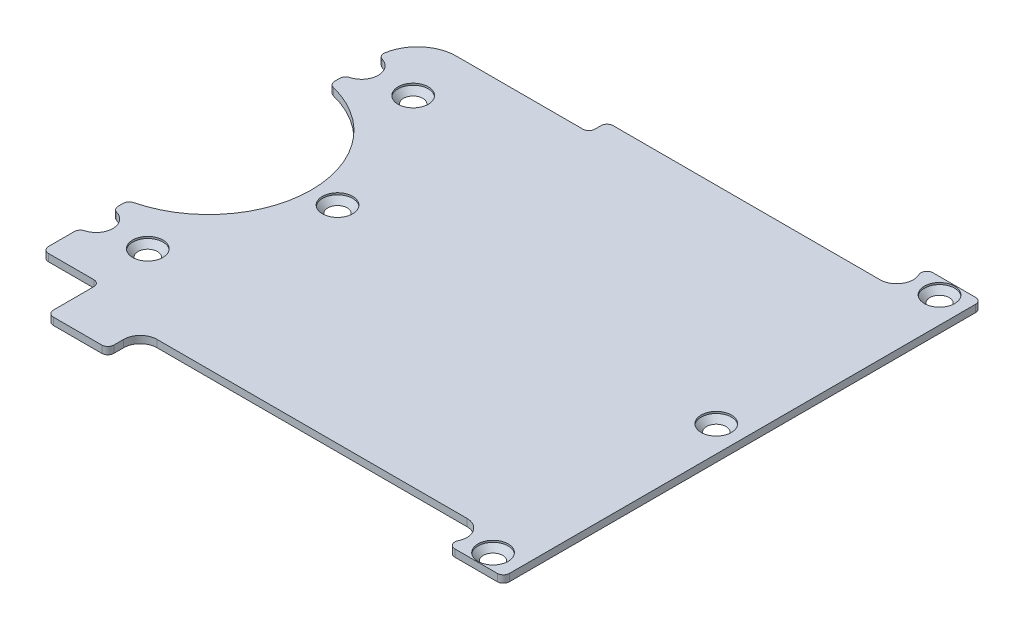
SolidWorks part; units mm, degrees
ref_plane "Front Plane" through (0, 0, 0) normal (0, 0, 1) x (1, 0, 0)
ref_plane "Top Plane" through (0, 0, 0) normal (0, 1, 0) x (1, 0, 0)
ref_plane "Right Plane" through (0, 0, 0) normal (1, 0, 0) x (0, 0, -1)
sketch "Sketch1" plane through (0, 0, 0) normal (0, 1, 0) x (1, 0, 0)
  line L0 (0, 30.3854) -> (0, -26.0557) construction
  line L1 (-19.0199, 0) -> (15.6179, 0) construction
  line L2 (-73.452, 57.1764) -> (-73.452, -39.7909) construction
  line L3 (0, 34.13) -> (-44.1, 34.13)
  line L4 (0, -34.13) -> (-51.202, -34.13)
  line L5 (-73.452, 19.17) -> (-73.452, 16.6626)
  line L6 (-53.952, -36.88) -> (-53.952, -39.5)
  line L7 (-63.952, -34.13) -> (-63.952, -39.5)
  line L8 (-73.452, -19.17) -> (-73.452, -16.6626)
  line L9 (11.4, 39.5) -> (11.4, -39.5)
  line L10 (11.4, 39.5) -> (0.8355, 39.5)
  line L11 (11.4, -39.5) -> (0.8355, -39.5)
  line L12 (-51.202, -34.13) -> (-73.452, -34.13) construction
  line L13 (-63.952, -39.5) -> (-52.0375, -39.5)
  line L14 (-73.452, -24.67) -> (-73.452, -30.8)
  line L15 (-63.952, 0) -> (-63.952, -34.13) construction
  line L16 (-73.452, -30.8) -> (-63.952, -30.8)
  line L17 (-63.952, -30.8) -> (-63.952, -34.13)
  line L18 (2.75, 36.88) -> (2.75, -36.88) construction
  line L19 (2.75, 36.88) -> (11.4, 36.88) construction
  line L20 (-73.452, 21.92) -> (11.4, 21.92) construction
  line L21 (7.075, 36.88) -> (7.075, -36.88) construction
  line L22 (-44.1, 34.13) -> (-44.1, -34.13) construction
  line L23 (-45.1, 33.13) -> (-45.1, 21.92) construction
  line L24 (-45.1, 33.13) -> (-44.1, 33.13) construction
  line L25 (-46.1, 31.13) -> (-66.992, 31.13)
  line L26 (-59.822, 0) -> (11.4, 0) construction
  line L27 (-73.452, 24.67) -> (-73.452, 31.13) construction
  line L28 (-45.1, 33.13) -> (-45.1, 32.13)
  line L29 (-24.211, 34.13) -> (-24.211, -34.13) construction
  circle A0 centre (0, 36.88) radius 2.5
  circle A1 centre (0, -36.88) radius 2.5
  circle A2 centre (-73.452, 21.92) radius 2.5
  circle A3 centre (-73.452, -21.92) radius 2.5
  circle A4 centre (-76.822, 0) radius 16
  circle A5 centre (-73.452, 21.92) radius 2.75
  circle A6 centre (-76.822, 0) radius 17
  circle A7 centre (-73.452, -21.92) radius 2.75
  circle A8 centre (0, 36.88) radius 2.75
  circle A9 centre (0, -36.88) radius 2.75
  arc A10 (-44.1, 34.13) -> (-45.1, 33.13) centre (-44.1, 33.13) ccw
  circle A11 centre (7.075, 36.88) radius 1
  circle A12 centre (7.075, -36.88) radius 1
  circle A13 centre (-64.925, 21.92) radius 1
  circle A14 centre (-64.925, -21.92) radius 1
  circle A15 centre (7.075, 0) radius 1
  circle A16 centre (-51.202, -36.88) radius 2.75
  arc A17 (-45.1, 32.13) -> (-46.1, 31.13) centre (-46.1, 32.13) cw
  arc A18 (-73.452, 24.67) -> (-66.992, 31.13) centre (-66.992, 24.67) cw
  circle A19 centre (-55.497, 0) radius 1
  point P39 (11.4, 0)
  point P77 (-59.822, 0)
  point P83 (-45.1, 31.13)
  point P86 (-24.211, 0)
  dimension "D2" = 5
  dimension "D3" = 43.84
  dimension "D5" = 32
  dimension "D16" = 2
  dimension "D20" = 1
  dimension "D1" = 73.76
  dimension "D4" = 74.96
  dimension "D6" = 3.37
  dimension "D12" = 79
  dimension "D13" = 11.4
  dimension "D9" = 10
  dimension "D10" = 55.5
  dimension "D11" = 5.37
  dimension "D14" = 8.7
  dimension "D15" = 9.5
  dimension "D17" = 72
  dimension "D18" = 1
  dimension "D7" = 0.25
  dimension "D8" = 1
extrude "Base shape" add sketch "Sketch1" along normal mid plane 1.2
fillet "Fillets" radius 1 14 edges at (-73.452, 0, -19.17) (-73.452, 0, -16.6626) (-73.452, 0, 24.67) (-73.452, 0, 19.17) (-73.452, 0, 16.6626) (-73.452, 0, 30.8) (-63.952, 0, 30.8) (0.8355, 0, -39.5) (0.8355, 0, 39.5) (11.4, 0, -39.5) (11.4, 0, 39.5) (-63.952, 0, 39.5) (-53.952, 0, 39.5) (-73.452, 0, -24.67)
hole_wizard "M2.5 countersunks" positions "Sketch2" profile "Sketch3" countersink size "M2" standard "ANSI Metric" end condition through all
sketch "Sketch2" plane through (0, -0.6, 0) normal (0, -1, 0) x (-1, 0, 0)
  point P0 (-7.075, 36.88)
  point P3 (-7.075, -36.88)
  point P6 (64.925, 21.92)
  point P9 (64.925, -21.92)
  point P13 (-7.075, 0)
  point P16 (55.497, 0)
sketch "Sketch3" plane through (7.075, -0.6, -36.88) normal (1, 0, 0) x (0, 0, -1)
  line L0 (0, 0) -> (0, 1.2)
  line L1 (0, 1.2) -> (1.25, 1.2)
  line L2 (1.25, 1.2) -> (1.25, 1.55)
  line L3 (1.25, 1.55) -> (2.5, 0.3)
  line L4 (2.5, 0.3) -> (2.5, 0)
  line L6 (2.5, 0) -> (0, 0)
  line L7 (-1.25, 1.55) -> (-2.5, 0.3) construction
  line L11 (0, -6.35) -> (0, 107.95) construction
  dimension "Thru Hole Dia." = 2.5
  dimension "Thru Hole Depth" = 1.2
  dimension "C'Sink Dia." = 5
  dimension "C'Sink Angle" = 90
  dimension "Head Clearance" = 0.3
mirror "Mirror1" about plane through (0, 0, 0) normal (0, 1, 0) of bodies 105
delete or keep bodies "Body-Delete/Keep 1" type delete bodies bodies 105
sketch "Sketch4" [suppressed] plane through (0, 0.5, 0) normal (0, 1, 0) x (1, 0, 0)
  line L13 (-73.452, 18.3058) -> (-73.452, 17.4615)
  line L14 (-73.452, -17.4615) -> (-73.452, -18.3058)
  line L15 (-73.452, -25.5342) -> (-73.452, -29.8)
  line L16 (-72.452, -30.8) -> (-64.952, -30.8)
  line L17 (-63.952, -31.8) -> (-63.952, -38.5)
  line L18 (-62.952, -39.5) -> (-54.952, -39.5)
  line L19 (-53.952, -38.5) -> (-53.952, -36.88)
  line L20 (-51.202, -34.13) -> (0, -34.13)
  line L21 (3.382, -39.5) -> (10.4, -39.5)
  line L22 (11.4, -38.5) -> (11.4, 38.5)
  line L23 (10.4, 39.5) -> (3.382, 39.5)
  line L24 (0, 34.13) -> (-42.6, 34.13)
  line L25 (-47.6, 29.13) -> (-68.992, 29.13)
  line L26 (-73.452, 18.3058) -> (-73.452, 17.4615)
  line L27 (-73.452, -17.4615) -> (-73.452, -18.3058)
  line L28 (-73.452, -25.5342) -> (-73.452, -29.8)
  line L29 (-72.452, -30.8) -> (-64.952, -30.8)
  line L30 (-63.952, -31.8) -> (-63.952, -38.5)
  line L31 (-62.952, -39.5) -> (-54.952, -39.5)
  line L32 (-53.952, -38.5) -> (-53.952, -36.88)
  line L33 (-51.202, -34.13) -> (0, -34.13)
  line L34 (3.382, -39.5) -> (10.4, -39.5)
  line L35 (11.4, -38.5) -> (11.4, 38.5)
  line L36 (10.4, 39.5) -> (3.382, 39.5)
  line L37 (0, 34.13) -> (-42.6, 34.13)
  line L38 (-47.6, 29.13) -> (-68.992, 29.13)
  circle A0 centre (-64.925, 21.92) radius 1 construction
  circle A1 centre (-55.822, 0) radius 1 construction
  circle A2 centre (-64.925, -21.92) radius 1 construction
  circle A3 centre (7.075, -36.88) radius 1 construction
  circle A4 centre (7.075, 0) radius 1 construction
  circle A5 centre (7.075, 36.88) radius 1 construction
  circle A6 centre (-64.925, 21.92) radius 1
  circle A7 centre (-55.822, 0) radius 1
  circle A8 centre (-64.925, -21.92) radius 1
  circle A9 centre (7.075, -36.88) radius 1
  circle A10 centre (7.075, 0) radius 1
  circle A11 centre (7.075, 36.88) radius 1
  arc A23 (-68.992, 29.13) -> (-73.3204, 25.7455) centre (-68.992, 24.67) ccw
  arc A24 (-73.3204, 25.7455) -> (-72.6438, 24.5486) centre (-72.3499, 25.5044) ccw
  arc A25 (-72.7187, 19.2696) -> (-72.6438, 24.5486) centre (-73.452, 21.92) ccw
  arc A26 (-72.7187, 19.2696) -> (-73.452, 18.3058) centre (-72.452, 18.3058) ccw
  arc A27 (-73.452, 17.4615) -> (-72.6948, 16.4914) centre (-72.452, 17.4615) ccw
  arc A28 (-72.6948, -16.4914) -> (-72.6948, 16.4914) centre (-76.822, 0) ccw
  arc A29 (-72.6948, -16.4914) -> (-73.452, -17.4615) centre (-72.452, -17.4615) ccw
  arc A30 (-73.452, -18.3058) -> (-72.7187, -19.2696) centre (-72.452, -18.3058) ccw
  arc A31 (-72.7187, -24.5704) -> (-72.7187, -19.2696) centre (-73.452, -21.92) ccw
  arc A32 (-72.7187, -24.5704) -> (-73.452, -25.5342) centre (-72.452, -25.5342) ccw
  arc A33 (-73.452, -29.8) -> (-72.452, -30.8) centre (-72.452, -29.8) ccw
  arc A34 (-63.952, -31.8) -> (-64.952, -30.8) centre (-64.952, -31.8) ccw
  arc A35 (-63.952, -38.5) -> (-62.952, -39.5) centre (-62.952, -38.5) ccw
  arc A36 (-54.952, -39.5) -> (-53.952, -38.5) centre (-54.952, -38.5) ccw
  arc A37 (-51.202, -34.13) -> (-53.952, -36.88) centre (-51.202, -36.88) ccw
  arc A38 (2.4802, -38.068) -> (0, -34.13) centre (0, -36.88) ccw
  arc A39 (2.4802, -38.068) -> (3.382, -39.5) centre (3.382, -38.5) ccw
  arc A40 (10.4, -39.5) -> (11.4, -38.5) centre (10.4, -38.5) ccw
  arc A41 (11.4, 38.5) -> (10.4, 39.5) centre (10.4, 38.5) ccw
  arc A42 (3.382, 39.5) -> (2.4802, 38.068) centre (3.382, 38.5) ccw
  arc A43 (0, 34.13) -> (2.4802, 38.068) centre (0, 36.88) ccw
  arc A44 (-42.6, 34.13) -> (-45.1, 31.63) centre (-42.6, 31.63) ccw
  arc A45 (-47.6, 29.13) -> (-45.1, 31.63) centre (-47.6, 31.63) ccw
  arc A46 (-68.992, 29.13) -> (-73.3204, 25.7455) centre (-68.992, 24.67) ccw
  arc A47 (-73.3204, 25.7455) -> (-72.6438, 24.5486) centre (-72.3499, 25.5044) ccw
  arc A48 (-72.7187, 19.2696) -> (-72.6438, 24.5486) centre (-73.452, 21.92) ccw
  arc A49 (-72.7187, 19.2696) -> (-73.452, 18.3058) centre (-72.452, 18.3058) ccw
  arc A50 (-73.452, 17.4615) -> (-72.6948, 16.4914) centre (-72.452, 17.4615) ccw
  arc A51 (-72.6948, -16.4914) -> (-72.6948, 16.4914) centre (-76.822, 0) ccw
  arc A52 (-72.6948, -16.4914) -> (-73.452, -17.4615) centre (-72.452, -17.4615) ccw
  arc A53 (-73.452, -18.3058) -> (-72.7187, -19.2696) centre (-72.452, -18.3058) ccw
  arc A54 (-72.7187, -24.5704) -> (-72.7187, -19.2696) centre (-73.452, -21.92) ccw
  arc A55 (-72.7187, -24.5704) -> (-73.452, -25.5342) centre (-72.452, -25.5342) ccw
  arc A56 (-73.452, -29.8) -> (-72.452, -30.8) centre (-72.452, -29.8) ccw
  arc A57 (-63.952, -31.8) -> (-64.952, -30.8) centre (-64.952, -31.8) ccw
  arc A58 (-63.952, -38.5) -> (-62.952, -39.5) centre (-62.952, -38.5) ccw
  arc A59 (-54.952, -39.5) -> (-53.952, -38.5) centre (-54.952, -38.5) ccw
  arc A60 (-51.202, -34.13) -> (-53.952, -36.88) centre (-51.202, -36.88) ccw
  arc A61 (2.4802, -38.068) -> (0, -34.13) centre (0, -36.88) ccw
  arc A62 (2.4802, -38.068) -> (3.382, -39.5) centre (3.382, -38.5) ccw
  arc A63 (10.4, -39.5) -> (11.4, -38.5) centre (10.4, -38.5) ccw
  arc A64 (11.4, 38.5) -> (10.4, 39.5) centre (10.4, 38.5) ccw
  arc A65 (3.382, 39.5) -> (2.4802, 38.068) centre (3.382, 38.5) ccw
  arc A66 (0, 34.13) -> (2.4802, 38.068) centre (0, 36.88) ccw
  arc A67 (-42.6, 34.13) -> (-45.1, 31.63) centre (-42.6, 31.63) ccw
  arc A68 (-47.6, 29.13) -> (-45.1, 31.63) centre (-47.6, 31.63) ccw
  dimension "D1" = 0
extrude "Core fill" [suppressed] add sketch "Sketch4" along normal offset from surface (9.2 mm away) 10.2
sketch "Sketch5" [suppressed] plane through (0, 9.45, 0) normal (0, 1, 0) x (1, 0, 0)
  line L0 (-46.1, 30.43) -> (-66.992, 30.43)
  line L1 (-72.752, 18.3058) -> (-72.752, 17.4615)
  line L2 (-72.752, -17.4615) -> (-72.752, -18.3058)
  line L3 (-72.752, -25.5342) -> (-72.752, -29.8)
  line L4 (-72.452, -30.1) -> (-64.952, -30.1)
  line L5 (-63.252, -31.8) -> (-63.252, -38.5)
  line L6 (-62.952, -38.8) -> (-54.952, -38.8)
  line L7 (-54.652, -38.5) -> (-54.652, -36.88)
  line L8 (-51.202, -33.43) -> (0, -33.43)
  line L9 (3.382, -38.8) -> (10.4, -38.8)
  line L10 (10.7, -38.5) -> (10.7, 38.5)
  line L11 (10.4, 38.8) -> (3.382, 38.8)
  line L12 (0, 33.43) -> (-44.1, 33.43)
  line L13 (-46.1, 31.13) -> (-66.992, 31.13)
  line L14 (-73.452, 18.3058) -> (-73.452, 17.4615)
  line L15 (-73.452, -17.4615) -> (-73.452, -18.3058)
  line L16 (-73.452, -25.5342) -> (-73.452, -29.8)
  line L17 (-72.452, -30.8) -> (-64.952, -30.8)
  line L18 (-63.952, -31.8) -> (-63.952, -38.5)
  line L19 (-62.952, -39.5) -> (-54.952, -39.5)
  line L20 (-53.952, -38.5) -> (-53.952, -36.88)
  line L21 (-51.202, -34.13) -> (0, -34.13)
  line L22 (3.382, -39.5) -> (10.4, -39.5)
  line L23 (11.4, -38.5) -> (11.4, 38.5)
  line L24 (10.4, 39.5) -> (3.382, 39.5)
  line L25 (0, 34.13) -> (-44.1, 34.13)
  line L26 (-46.1, 31.13) -> (-66.992, 31.13)
  line L27 (-73.452, 18.3058) -> (-73.452, 17.4615)
  line L28 (-73.452, -17.4615) -> (-73.452, -18.3058)
  line L29 (-73.452, -25.5342) -> (-73.452, -29.8)
  line L30 (-72.452, -30.8) -> (-64.952, -30.8)
  line L31 (-63.952, -31.8) -> (-63.952, -38.5)
  line L32 (-62.952, -39.5) -> (-54.952, -39.5)
  line L33 (-53.952, -38.5) -> (-53.952, -36.88)
  line L34 (-51.202, -34.13) -> (0, -34.13)
  line L35 (3.382, -39.5) -> (10.4, -39.5)
  line L36 (11.4, -38.5) -> (11.4, 38.5)
  line L37 (10.4, 39.5) -> (3.382, 39.5)
  line L38 (0, 34.13) -> (-44.1, 34.13)
  line L39 (-66.992, 31.13) -> (-66.992, 30.43) construction
  line L40 (-63.025, 21.92) -> (-62.325, 21.92) construction
  line L41 (-67.525, 21.92) -> (-70.002, 21.92) construction
  line L42 (-64.925, 24.52) -> (-64.925, 30.43) construction
  line L43 (-64.925, 19.32) -> (-64.925, 13.1054) construction
  line L44 (-65.275, 30.4537) -> (-64.575, 30.4537)
  line L45 (-65.275, 30.4537) -> (-65.275, 24.4963)
  line L46 (-65.275, 24.4963) -> (-64.575, 24.4963)
  line L47 (-64.575, 30.4537) -> (-64.575, 24.4963)
  line L48 (-65.275, 30.4537) -> (-64.575, 24.4963) construction
  line L49 (-65.275, 24.4963) -> (-64.575, 30.4537) construction
  line L50 (-70.0257, 22.27) -> (-67.5013, 22.27)
  line L51 (-70.0257, 22.27) -> (-70.0257, 21.57)
  line L52 (-70.0257, 21.57) -> (-67.5013, 21.57)
  line L53 (-67.5013, 22.27) -> (-67.5013, 21.57)
  line L54 (-70.0257, 22.27) -> (-67.5013, 21.57) construction
  line L55 (-70.0257, 21.57) -> (-67.5013, 22.27) construction
  line L56 (-10.5773, 0) -> (21.3129, 0) construction
  line L57 (-65.275, 19.6465) -> (-64.575, 19.6465)
  line L58 (-65.275, 19.6465) -> (-65.275, 12.7789)
  line L59 (-65.275, 12.7789) -> (-64.575, 12.7789)
  line L60 (-64.575, 19.6465) -> (-64.575, 12.7789)
  line L61 (-65.275, 19.6465) -> (-64.575, 12.7789) construction
  line L62 (-65.275, 12.7789) -> (-64.575, 19.6465) construction
  line L63 (4.475, 36.88) -> (3.45, 36.88) construction
  line L68 (-52.897, 0) -> (4.475, 0) construction
  line L69 (-24.211, 0) -> (-24.211, 33.43) construction
  line L70 (9.675, 36.88) -> (10.7, 36.88) construction
  line L71 (-55.497, 2.6) -> (-59.314, 2.6)
  line L72 (3.4263, 37.23) -> (4.4987, 37.23)
  line L73 (3.4263, 37.23) -> (3.4263, 36.53)
  line L74 (3.4263, 36.53) -> (4.4987, 36.53)
  line L75 (4.4987, 37.23) -> (4.4987, 36.53)
  line L76 (3.4263, 37.23) -> (4.4987, 36.53) construction
  line L77 (3.4263, 36.53) -> (4.4987, 37.23) construction
  line L78 (10.7237, 37.23) -> (9.6513, 37.23)
  line L79 (10.7237, 37.23) -> (10.7237, 36.53)
  line L80 (10.7237, 36.53) -> (9.6513, 36.53)
  line L81 (9.6513, 37.23) -> (9.6513, 36.53)
  line L82 (10.7237, 37.23) -> (9.6513, 36.53) construction
  line L83 (10.7237, 36.53) -> (9.6513, 37.23) construction
  line L84 (-59.2243, 1.9) -> (-57.2718, 1.9)
  line L85 (10.7237, -36.53) -> (9.6513, -36.53)
  line L86 (10.7237, -37.23) -> (9.6513, -37.23)
  line L87 (3.4263, -37.23) -> (4.4987, -37.23)
  line L88 (3.4263, -36.53) -> (4.4987, -36.53)
  line L89 (-70.0257, -22.27) -> (-67.5013, -22.27)
  line L90 (-70.0257, -21.57) -> (-67.5013, -21.57)
  line L91 (-65.275, -19.6465) -> (-65.275, -12.7789)
  line L92 (-64.575, -19.6465) -> (-64.575, -12.7789)
  line L93 (-64.925, -21.92) -> (-64.952, -31.8) construction
  line L95 (-55.497, -2.6) -> (-59.314, -2.6)
  line L96 (-59.2243, -1.9) -> (-57.2718, -1.9)
  line L97 (-65.2898, -30.139) -> (-64.5898, -30.139)
  line L98 (-65.2898, -30.139) -> (-65.2898, -24.4983)
  line L99 (-65.2898, -24.4983) -> (-64.5898, -24.4983)
  line L100 (-64.5898, -30.139) -> (-64.5898, -24.4983)
  line L101 (-65.2898, -30.139) -> (-64.5898, -24.4983) construction
  line L102 (-65.2898, -24.4983) -> (-64.5898, -30.139) construction
  line L105 (4.4987, -0.35) -> (-52.9207, -0.35)
  line L106 (4.4987, -0.35) -> (4.4987, 0.35)
  line L107 (4.4987, 0.35) -> (-52.9207, 0.35)
  line L108 (-52.9207, -0.35) -> (-52.9207, 0.35)
  line L109 (4.4987, -0.35) -> (-52.9207, 0.35) construction
  line L110 (4.4987, 0.35) -> (-52.9207, -0.35) construction
  line L111 (7.075, 2.6) -> (10.892, 2.6)
  line L112 (10.8023, 1.9) -> (8.8498, 1.9)
  line L113 (10.8023, -1.9) -> (8.8498, -1.9)
  line L114 (7.075, -2.6) -> (10.892, -2.6)
  line L115 (-45.1, 33.13) -> (-45.1, 32.13) construction
  line L116 (-45.1, 33.13) -> (-45.1, 32.13)
  line L118 (-45.1, 33.13) -> (-45.1, 32.13)
  line L119 (-44.4, 33.13) -> (-44.4, 32.13)
  circle A0 centre (-64.925, 21.92) radius 1.9
  arc A1 (-66.992, 30.43) -> (-72.6826, 25.5618) centre (-66.992, 24.67) ccw
  arc A2 (-72.6826, 25.5618) -> (-72.4715, 25.2277) centre (-72.3862, 25.5153) ccw
  arc A3 (-72.532, 18.5949) -> (-72.4715, 25.2277) centre (-73.452, 21.92) ccw
  arc A4 (-72.532, 18.5949) -> (-72.752, 18.3058) centre (-72.452, 18.3058) ccw
  arc A5 (-72.752, 17.4615) -> (-72.5249, 17.1705) centre (-72.452, 17.4615) ccw
  arc A6 (-72.5249, -17.1705) -> (-72.5249, 17.1705) centre (-76.822, 0) ccw
  arc A7 (-72.5249, -17.1705) -> (-72.752, -17.4615) centre (-72.452, -17.4615) ccw
  arc A8 (-72.752, -18.3058) -> (-72.532, -18.5949) centre (-72.452, -18.3058) ccw
  arc A9 (-72.532, -25.2451) -> (-72.532, -18.5949) centre (-73.452, -21.92) ccw
  arc A10 (-72.532, -25.2451) -> (-72.752, -25.5342) centre (-72.452, -25.5342) ccw
  arc A11 (-72.752, -29.8) -> (-72.452, -30.1) centre (-72.452, -29.8) ccw
  arc A12 (-63.252, -31.8) -> (-64.952, -30.1) centre (-64.952, -31.8) ccw
  arc A13 (-63.252, -38.5) -> (-62.952, -38.8) centre (-62.952, -38.5) ccw
  arc A14 (-54.952, -38.8) -> (-54.652, -38.5) centre (-54.952, -38.5) ccw
  arc A15 (-51.202, -33.43) -> (-54.652, -36.88) centre (-51.202, -36.88) ccw
  arc A16 (3.1115, -38.3704) -> (0, -33.43) centre (0, -36.88) ccw
  arc A17 (3.1115, -38.3704) -> (3.382, -38.8) centre (3.382, -38.5) ccw
  arc A18 (10.4, -38.8) -> (10.7, -38.5) centre (10.4, -38.5) ccw
  arc A19 (10.7, 38.5) -> (10.4, 38.8) centre (10.4, 38.5) ccw
  arc A20 (3.382, 38.8) -> (3.1115, 38.3704) centre (3.382, 38.5) ccw
  arc A21 (0, 33.43) -> (3.1115, 38.3704) centre (0, 36.88) ccw
  arc A23 (-66.992, 31.13) -> (-73.3741, 25.6702) centre (-66.992, 24.67) ccw
  arc A24 (-73.3741, 25.6702) -> (-72.6704, 24.5566) centre (-72.3862, 25.5153) ccw
  arc A25 (-72.7187, 19.2696) -> (-72.6704, 24.5566) centre (-73.452, 21.92) ccw
  arc A26 (-72.7187, 19.2696) -> (-73.452, 18.3058) centre (-72.452, 18.3058) ccw
  arc A27 (-73.452, 17.4615) -> (-72.6948, 16.4914) centre (-72.452, 17.4615) ccw
  arc A28 (-72.6948, -16.4914) -> (-72.6948, 16.4914) centre (-76.822, 0) ccw
  arc A29 (-72.6948, -16.4914) -> (-73.452, -17.4615) centre (-72.452, -17.4615) ccw
  arc A30 (-73.452, -18.3058) -> (-72.7187, -19.2696) centre (-72.452, -18.3058) ccw
  arc A31 (-72.7187, -24.5704) -> (-72.7187, -19.2696) centre (-73.452, -21.92) ccw
  arc A32 (-72.7187, -24.5704) -> (-73.452, -25.5342) centre (-72.452, -25.5342) ccw
  arc A33 (-73.452, -29.8) -> (-72.452, -30.8) centre (-72.452, -29.8) ccw
  arc A34 (-63.952, -31.8) -> (-64.952, -30.8) centre (-64.952, -31.8) ccw
  arc A35 (-63.952, -38.5) -> (-62.952, -39.5) centre (-62.952, -38.5) ccw
  arc A36 (-54.952, -39.5) -> (-53.952, -38.5) centre (-54.952, -38.5) ccw
  arc A37 (-51.202, -34.13) -> (-53.952, -36.88) centre (-51.202, -36.88) ccw
  arc A38 (2.4802, -38.068) -> (0, -34.13) centre (0, -36.88) ccw
  arc A39 (2.4802, -38.068) -> (3.382, -39.5) centre (3.382, -38.5) ccw
  arc A40 (10.4, -39.5) -> (11.4, -38.5) centre (10.4, -38.5) ccw
  arc A41 (11.4, 38.5) -> (10.4, 39.5) centre (10.4, 38.5) ccw
  arc A42 (3.382, 39.5) -> (2.4802, 38.068) centre (3.382, 38.5) ccw
  arc A43 (0, 34.13) -> (2.4802, 38.068) centre (0, 36.88) ccw
  arc A44 (-44.1, 34.13) -> (-45.1, 33.13) centre (-44.1, 33.13) ccw
  arc A45 (-46.1, 31.13) -> (-45.1, 32.13) centre (-46.1, 32.13) ccw
  arc A46 (-66.992, 31.13) -> (-73.3741, 25.6702) centre (-66.992, 24.67) ccw
  arc A47 (-73.3741, 25.6702) -> (-72.6704, 24.5566) centre (-72.3862, 25.5153) ccw
  arc A48 (-72.7187, 19.2696) -> (-72.6704, 24.5566) centre (-73.452, 21.92) ccw
  arc A49 (-72.7187, 19.2696) -> (-73.452, 18.3058) centre (-72.452, 18.3058) ccw
  arc A50 (-73.452, 17.4615) -> (-72.6948, 16.4914) centre (-72.452, 17.4615) ccw
  arc A51 (-72.6948, -16.4914) -> (-72.6948, 16.4914) centre (-76.822, 0) ccw
  arc A52 (-72.6948, -16.4914) -> (-73.452, -17.4615) centre (-72.452, -17.4615) ccw
  arc A53 (-73.452, -18.3058) -> (-72.7187, -19.2696) centre (-72.452, -18.3058) ccw
  arc A54 (-72.7187, -24.5704) -> (-72.7187, -19.2696) centre (-73.452, -21.92) ccw
  arc A55 (-72.7187, -24.5704) -> (-73.452, -25.5342) centre (-72.452, -25.5342) ccw
  arc A56 (-73.452, -29.8) -> (-72.452, -30.8) centre (-72.452, -29.8) ccw
  arc A57 (-63.952, -31.8) -> (-64.952, -30.8) centre (-64.952, -31.8) ccw
  arc A58 (-63.952, -38.5) -> (-62.952, -39.5) centre (-62.952, -38.5) ccw
  arc A59 (-54.952, -39.5) -> (-53.952, -38.5) centre (-54.952, -38.5) ccw
  arc A60 (-51.202, -34.13) -> (-53.952, -36.88) centre (-51.202, -36.88) ccw
  arc A61 (2.4802, -38.068) -> (0, -34.13) centre (0, -36.88) ccw
  arc A62 (2.4802, -38.068) -> (3.382, -39.5) centre (3.382, -38.5) ccw
  arc A63 (10.4, -39.5) -> (11.4, -38.5) centre (10.4, -38.5) ccw
  arc A64 (11.4, 38.5) -> (10.4, 39.5) centre (10.4, 38.5) ccw
  arc A65 (3.382, 39.5) -> (2.4802, 38.068) centre (3.382, 38.5) ccw
  arc A66 (0, 34.13) -> (2.4802, 38.068) centre (0, 36.88) ccw
  circle A70 centre (-64.925, 21.92) radius 2.6
  circle A71 centre (-55.497, 0) radius 1.9
  circle A73 centre (7.075, 0) radius 1.9
  circle A74 centre (7.075, 36.88) radius 1.9
  circle A76 centre (7.075, 36.88) radius 2.6
  circle A77 centre (7.075, 0) radius 2.6
  circle A80 centre (-55.497, 0) radius 2.6
  circle A81 centre (7.075, -36.88) radius 2.6
  circle A82 centre (7.075, -36.88) radius 1.9
  circle A83 centre (-64.925, -21.92) radius 1.9
  circle A84 centre (-64.925, -21.92) radius 2.6
  arc A92 (-46.1, 31.13) -> (-45.1, 32.13) centre (-46.1, 32.13) ccw construction
  arc A93 (-44.1, 34.13) -> (-45.1, 33.13) centre (-44.1, 33.13) ccw construction
  arc A94 (-46.1, 31.13) -> (-45.1, 32.13) centre (-46.1, 32.13) ccw
  arc A95 (-44.1, 34.13) -> (-45.1, 33.13) centre (-44.1, 33.13) ccw
  arc A96 (-44.1, 33.43) -> (-44.4, 33.13) centre (-44.1, 33.13) ccw
  arc A97 (-46.1, 30.43) -> (-44.4, 32.13) centre (-46.1, 32.13) ccw
  arc A108 (-46.1, 31.13) -> (-45.1, 33.13) centre (-46.1, 32.38) ccw construction
  arc A110 (-46.1, 30.43) -> (-44.3651, 33.2704) centre (-46.1, 32.38) ccw construction
  arc A111 (-44.1, 33.43) -> (-44.3651, 33.2704) centre (-44.1, 33.13) ccw construction
  arc A115 (-44.1, 34.13) -> (-45.1, 33.13) centre (-44.1, 33.13) ccw construction
  point P129 (-64.925, 27.475)
  point P145 (-68.7635, 21.92)
  point P152 (-64.925, 16.2127)
  point P162 (-24.211, 0)
  point P169 (3.9625, 36.88)
  point P174 (10.1875, 36.88)
  point P183 (-64.9398, -27.3187)
  point P185 (-55.497, 1.9)
  dimension "D2" = 3.75
  dimension "D1" = 0
  dimension "D3" = 0.7
extrude "Core walls" [suppressed] cut sketch "Sketch5" against normal up to next
sketch "Sketch6" [suppressed] plane through (0, -0.75, 0) normal (0, -1, 0) x (1, 0, 0)
  line L0 (-62.952, 38.8) -> (-54.952, 38.8) construction
  line L1 (-60.252, 38.8) -> (-63.252, 38.8)
  line L2 (-60.252, 38.8) -> (-60.252, 31.8)
  line L3 (-60.252, 31.8) -> (-63.252, 31.8)
  line L4 (-63.252, 38.8) -> (-63.252, 31.8)
  dimension "D1" = 3
extrude "XT30 fill" [suppressed] add sketch "Sketch6" against normal up to surface (10.2 mm away)
sketch "Sketch7" [suppressed] plane through (-63.952, 0, 0) normal (-1, 0, 0) x (0, 0, 1)
  line L0 (31.8, 9.45) -> (38.5, 9.45) construction
  line L1 (38.2, 9.45) -> (32.6, 9.45)
  line L2 (38.2, 9.45) -> (38.2, -0.75)
  line L3 (38.2, -0.75) -> (32.6, -0.75)
  line L4 (32.6, 9.45) -> (32.6, -0.75)
  line L5 (31.8, -0.75) -> (38.5, -0.75) construction
  line L6 (39.5, 9.45) -> (39.5, -0.75) construction
  line L7 (32.6, 0.25) -> (33.6, -0.75)
  line L8 (35.4, 9.45) -> (35.4, -0.75) construction
  line L9 (38.2, 0.25) -> (37.2, -0.75)
  line L11 (33.3, -0.45) -> (37.5, -0.45)
  line L12 (33.3, -0.45) -> (33.3, -0.75)
  line L13 (33.3, -0.75) -> (37.5, -0.75)
  line L14 (37.5, -0.45) -> (37.5, -0.75)
  line L15 (33.3, -0.45) -> (37.5, -0.75) construction
  line L16 (33.3, -0.75) -> (37.5, -0.45) construction
  point P16 (35.4, -0.6)
  line M9 (38.5, 9.45) -> (31.8, 9.45)
  dimension "D1" = 5.6
  dimension "D2" = 1.3
  dimension "D3" = 45
  dimension "D4" = 1
  dimension "D5" = 0.7
extrude "XT30 cut" [suppressed] cut sketch "Sketch7" against normal up to next contours L7 L11 L9 L2 L4 M9
sketch "Sketch8" [suppressed] plane through (0, -0.75, 0) normal (0, -1, 0) x (1, 0, 0)
  line L0 (-63.252, 31.8) -> (-63.252, 32.6) construction
  line L1 (-60.252, 31.8) -> (-59.452, 31.8)
  line L2 (-60.252, 31.8) -> (-60.252, 33.3)
  line L3 (-60.252, 33.3) -> (-59.452, 33.3)
  line L4 (-59.452, 31.8) -> (-59.452, 33.3)
  line L5 (-60.252, 32.6) -> (-63.952, 32.6) construction
  line L6 (-60.252, 33.3) -> (-63.952, 33.3) construction
  line L7 (-60.252, 37.5) -> (-63.952, 37.5) construction
  line L9 (-60.252, 38.8) -> (-59.452, 38.8)
  line L10 (-60.252, 38.8) -> (-60.252, 37.5)
  line L11 (-60.252, 37.5) -> (-59.452, 37.5)
  line L12 (-59.452, 38.8) -> (-59.452, 37.5)
extrude "XT30 rear support" [suppressed] add sketch "Sketch8" against normal up to surface (10.2 mm away)
sketch "Sketch9" [suppressed] plane through (0, -0.75, 0) normal (0, -1, 0) x (1, 0, 0)
  line L0 (-63.952, 38.2) -> (-63.952, 32.6)
  line L1 (-44.4, -34.0839) -> (-44.4, 34.13)
  line L2 (-63.952, 31.8) -> (-63.952, 32.6) construction
  line L3 (-63.952, 38.2) -> (-63.952, 38.5) construction
  line L4 (-62.952, 39.5) -> (-54.952, 39.5) construction
  line L5 (-53.952, 38.5) -> (-53.952, 36.88) construction
  line L6 (-51.202, 34.13) -> (0, 34.13) construction
  line L7 (3.382, 39.5) -> (10.4, 39.5) construction
  line L8 (11.4, 38.5) -> (11.4, -38.5) construction
  line L9 (10.4, -39.5) -> (3.382, -39.5) construction
  line L10 (0, -34.13) -> (-44.1, -34.13) construction
  line L11 (-46.1, -31.13) -> (-66.992, -31.13) construction
  line L12 (-73.452, -18.3058) -> (-73.452, -17.4615) construction
  line L13 (-73.452, 17.4615) -> (-73.452, 18.3058) construction
  line L14 (-73.452, 25.5342) -> (-73.452, 29.8) construction
  line L15 (-72.452, 30.8) -> (-64.952, 30.8) construction
  line L16 (-63.952, 31.8) -> (-63.952, 32.6)
  line L17 (-63.952, 38.2) -> (-63.952, 38.5)
  line L18 (-62.952, 39.5) -> (-54.952, 39.5)
  line L19 (-53.952, 38.5) -> (-53.952, 36.88)
  line L20 (-51.202, 34.13) -> (0, 34.13)
  line L21 (3.382, 39.5) -> (10.4, 39.5)
  line L22 (11.4, 38.5) -> (11.4, -38.5)
  line L23 (10.4, -39.5) -> (3.382, -39.5)
  line L24 (0, -34.13) -> (-44.1, -34.13)
  line L25 (-46.1, -31.13) -> (-66.992, -31.13)
  line L26 (-73.452, -18.3058) -> (-73.452, -17.4615)
  line L27 (-73.452, 17.4615) -> (-73.452, 18.3058)
  line L28 (-73.452, 25.5342) -> (-73.452, 29.8)
  line L29 (-72.452, 30.8) -> (-64.952, 30.8)
  line L30 (-45.1, -33.13) -> (-45.1, -32.13) construction
  line L31 (-45.1, -33.13) -> (-45.1, -32.13)
  line L33 (-44.4, -33.13) -> (-44.4, -32.13) construction
  line L34 (-60.252, 32.6) -> (-60.252, 38.2)
  line L37 (-60.252, 38.2) -> (-63.952, 38.2)
  line L38 (-60.252, 32.6) -> (-63.952, 32.6)
  arc A0 (-64.952, 30.8) -> (-63.952, 31.8) centre (-64.952, 31.8) ccw construction
  arc A1 (-62.952, 39.5) -> (-63.952, 38.5) centre (-62.952, 38.5) ccw construction
  arc A2 (-53.952, 38.5) -> (-54.952, 39.5) centre (-54.952, 38.5) ccw construction
  arc A3 (-53.952, 36.88) -> (-51.202, 34.13) centre (-51.202, 36.88) ccw construction
  arc A4 (0, 34.13) -> (2.4802, 38.068) centre (0, 36.88) ccw construction
  arc A5 (3.382, 39.5) -> (2.4802, 38.068) centre (3.382, 38.5) ccw construction
  arc A6 (11.4, 38.5) -> (10.4, 39.5) centre (10.4, 38.5) ccw construction
  arc A7 (10.4, -39.5) -> (11.4, -38.5) centre (10.4, -38.5) ccw construction
  arc A8 (2.4802, -38.068) -> (3.382, -39.5) centre (3.382, -38.5) ccw construction
  arc A9 (2.4802, -38.068) -> (0, -34.13) centre (0, -36.88) ccw construction
  arc A10 (-45.1, -33.13) -> (-44.1, -34.13) centre (-44.1, -33.13) ccw construction
  circle A11 centre (-64.925, -21.92) radius 1.9 construction
  arc A12 (-73.3741, -25.6702) -> (-66.992, -31.13) centre (-66.992, -24.67) ccw construction
  arc A13 (-72.6704, -24.5566) -> (-73.3741, -25.6702) centre (-72.3862, -25.5153) ccw construction
  arc A14 (-72.6704, -24.5566) -> (-72.7187, -19.2696) centre (-73.452, -21.92) ccw construction
  arc A15 (-73.452, -18.3058) -> (-72.7187, -19.2696) centre (-72.452, -18.3058) ccw construction
  arc A16 (-72.6948, -16.4914) -> (-73.452, -17.4615) centre (-72.452, -17.4615) ccw construction
  arc A17 (-72.6948, -16.4914) -> (-72.6948, 16.4914) centre (-76.822, 0) ccw construction
  arc A18 (-73.452, 17.4615) -> (-72.6948, 16.4914) centre (-72.452, 17.4615) ccw construction
  arc A19 (-72.7187, 19.2696) -> (-73.452, 18.3058) centre (-72.452, 18.3058) ccw construction
  arc A20 (-72.7187, 19.2696) -> (-72.7187, 24.5704) centre (-73.452, 21.92) ccw construction
  arc A21 (-73.452, 25.5342) -> (-72.7187, 24.5704) centre (-72.452, 25.5342) ccw construction
  arc A22 (-72.452, 30.8) -> (-73.452, 29.8) centre (-72.452, 29.8) ccw construction
  arc A23 (-64.952, 30.8) -> (-63.952, 31.8) centre (-64.952, 31.8) ccw
  arc A24 (-62.952, 39.5) -> (-63.952, 38.5) centre (-62.952, 38.5) ccw
  arc A25 (-53.952, 38.5) -> (-54.952, 39.5) centre (-54.952, 38.5) ccw
  arc A26 (-53.952, 36.88) -> (-51.202, 34.13) centre (-51.202, 36.88) ccw
  arc A27 (0, 34.13) -> (2.4802, 38.068) centre (0, 36.88) ccw
  arc A28 (3.382, 39.5) -> (2.4802, 38.068) centre (3.382, 38.5) ccw
  arc A29 (11.4, 38.5) -> (10.4, 39.5) centre (10.4, 38.5) ccw
  arc A30 (10.4, -39.5) -> (11.4, -38.5) centre (10.4, -38.5) ccw
  arc A31 (2.4802, -38.068) -> (3.382, -39.5) centre (3.382, -38.5) ccw
  arc A32 (2.4802, -38.068) -> (0, -34.13) centre (0, -36.88) ccw
  arc A33 (-45.1, -33.13) -> (-44.1, -34.13) centre (-44.1, -33.13) ccw
  arc A35 (-73.3741, -25.6702) -> (-66.992, -31.13) centre (-66.992, -24.67) ccw
  arc A36 (-72.6704, -24.5566) -> (-73.3741, -25.6702) centre (-72.3862, -25.5153) ccw
  arc A37 (-72.6704, -24.5566) -> (-72.7187, -19.2696) centre (-73.452, -21.92) ccw
  arc A38 (-73.452, -18.3058) -> (-72.7187, -19.2696) centre (-72.452, -18.3058) ccw
  arc A39 (-72.6948, -16.4914) -> (-73.452, -17.4615) centre (-72.452, -17.4615) ccw
  arc A40 (-72.6948, -16.4914) -> (-72.6948, 16.4914) centre (-76.822, 0) ccw
  arc A41 (-73.452, 17.4615) -> (-72.6948, 16.4914) centre (-72.452, 17.4615) ccw
  arc A42 (-72.7187, 19.2696) -> (-73.452, 18.3058) centre (-72.452, 18.3058) ccw
  arc A43 (-72.7187, 19.2696) -> (-72.7187, 24.5704) centre (-73.452, 21.92) ccw
  arc A44 (-73.452, 25.5342) -> (-72.7187, 24.5704) centre (-72.452, 25.5342) ccw
  arc A45 (-72.452, 30.8) -> (-73.452, 29.8) centre (-72.452, 29.8) ccw
  arc A46 (-45.1, -32.13) -> (-46.1, -31.13) centre (-46.1, -32.13) ccw construction
  arc A47 (-45.1, -32.13) -> (-46.1, -31.13) centre (-46.1, -32.13) ccw
  circle A48 centre (-64.925, -21.92) radius 1.9
  circle A49 centre (-55.497, 0) radius 1.9 construction
  circle A50 centre (-55.497, 0) radius 1.9
  circle A51 centre (-64.925, 21.92) radius 1.9 construction
  circle A52 centre (-64.925, 21.92) radius 1.9
extrude "Floor" [suppressed] add sketch "Sketch9" against normal blind 0.7
sketch "Sketch10" [suppressed] plane through (0, -0.05, 0) normal (0, 1, 0) x (1, 0, 0)
  line L0 (-44.4, 32.13) -> (-44.4, 30.43)
  line L1 (-64.575, 30.43) -> (-44.4, 30.43)
  line L2 (-64.575, 30.43) -> (-64.575, 12.78)
  line L3 (-64.575, 12.78) -> (-44.4, 12.78)
  line L4 (-44.4, 30.43) -> (-44.4, 12.78)
  line L5 (-44.4, 32.13) -> (-44.4, 0.35) construction
  arc A1 (-46.1, 30.43) -> (-44.4, 32.13) centre (-46.1, 32.13) ccw construction
  arc A2 (-59.314, 2.6) -> (-64.575, 12.7789) centre (-76.822, 0) ccw construction
  arc A3 (-59.314, 2.6) -> (-64.575, 12.7789) centre (-76.822, 0) ccw
  arc A4 (-46.1, 30.43) -> (-44.4, 32.13) centre (-46.1, 32.13) ccw
  dimension "D1" = 17.65
extrude "Balance fill" [suppressed] add sketch "Sketch10" along normal up to surface (9.5 mm away)
sketch "Sketch11" [suppressed] plane through (0, 9.45, 0) normal (0, 1, 0) x (1, 0, 0)
  line L0 (-46.1, 31.13) -> (-46.1, 12.78) construction
  line L1 (-64.575, 12.78) -> (-44.4, 12.78) construction
  line L2 (-63.025, 31.13) -> (-63.025, 12.78) construction
  line L3 (-46.1, 31.13) -> (-66.992, 31.13) construction
  line L4 (-63.025, 22.38) -> (-46.1, 22.38) construction
  line L6 (-62.7625, 13.63) -> (-46.3625, 13.63)
  line L7 (-62.7625, 13.63) -> (-62.7625, 31.13)
  line L8 (-62.7625, 31.13) -> (-46.3625, 31.13)
  line L9 (-46.3625, 13.63) -> (-46.3625, 31.13)
  line L10 (-62.7625, 13.63) -> (-46.3625, 31.13) construction
  line L11 (-62.7625, 31.13) -> (-46.3625, 13.63) construction
  circle A0 centre (-64.925, 21.92) radius 1.9 construction
  point P14 (-54.5625, 22.38)
  dimension "D1" = 16.4
  dimension "D2" = 17.5
extrude "Balance cut" [suppressed] cut sketch "Sketch11" against normal blind 5.6
sketch "Sketch12" [suppressed] plane through (0, 3.85, 0) normal (0, 1, 0) x (1, 0, 0)
  line L0 (-54.5625, 31.13) -> (-54.5625, 13.63) construction
  line L1 (-46.3625, 31.13) -> (-62.7625, 31.13) construction
  line L2 (-62.7625, 13.63) -> (-46.3625, 13.63) construction
  line L3 (-62.7625, 22.63) -> (-46.3625, 22.63)
  line L4 (-62.7625, 31.13) -> (-62.7625, 13.63) construction
  line L5 (-46.3625, 13.63) -> (-46.3625, 31.13) construction
  line L6 (-62.7625, 13.63) -> (-46.3625, 13.63) construction
  line L7 (-60.5625, 13.63) -> (-48.5625, 13.63)
  line L8 (-60.5625, 13.63) -> (-60.5625, 22.63)
  line L9 (-60.5625, 22.63) -> (-48.5625, 22.63)
  line L10 (-48.5625, 13.63) -> (-48.5625, 22.63)
  line L11 (-60.5625, 13.63) -> (-48.5625, 22.63) construction
  line L12 (-60.5625, 22.63) -> (-48.5625, 13.63) construction
  line L13 (-46.3625, 13.63) -> (-46.3625, 31.13) construction
  line L14 (-62.7625, 31.13) -> (-46.3625, 31.13)
  line L15 (-62.7625, 31.13) -> (-62.7625, 22.63)
  line L16 (-62.7625, 22.63) -> (-46.3625, 22.63)
  line L17 (-46.3625, 31.13) -> (-46.3625, 22.63)
  line L18 (-62.7625, 13.63) -> (-46.3625, 13.63)
  line L19 (-62.7625, 13.63) -> (-62.7625, 15.13)
  line L20 (-62.7625, 15.13) -> (-46.3625, 15.13)
  line L21 (-46.3625, 13.63) -> (-46.3625, 15.13)
  point P12 (-54.5625, 18.13)
  line M11 (-46.3625, 13.63) -> (-46.3625, 31.13)
  line M12 (-46.3625, 31.13) -> (-62.7625, 31.13)
  line M13 (-62.7625, 31.13) -> (-62.7625, 13.63)
  dimension "D1" = 9
  dimension "D2" = 12
  dimension "D3" = 1.5
extrude "Balance bottom" [suppressed] add sketch "Sketch12" along normal blind 0.5 contours L3 M13 M11 M12 | L8 L20 L10 L3
sketch "Sketch13" [suppressed] plane through (0, 0, -31.13) normal (0, 0, -1) x (-1, 0, 0)
  line L0 (54.5625, 4.35) -> (54.5625, -0.75) construction
  line L1 (46.3625, 4.35) -> (62.7625, 4.35) construction
  line L2 (46.1, -0.75) -> (66.992, -0.75) construction
  line L4 (51.8625, 1.35) -> (57.2625, 1.35)
  line L5 (51.8625, 1.35) -> (51.8625, 4.35)
  line L6 (51.8625, 4.35) -> (57.2625, 4.35)
  line L7 (57.2625, 1.35) -> (57.2625, 4.35)
  line L8 (51.8625, 1.35) -> (57.2625, 4.35) construction
  line L9 (51.8625, 4.35) -> (57.2625, 1.35) construction
  point P6 (54.5625, 2.85)
  dimension "D1" = 3
  dimension "D2" = 5.4
extrude "Balance fixer cut" [suppressed] cut sketch "Sketch13" against normal blind 6.25
sketch "Sketch14" [suppressed] plane through (0, 0, -13.63) normal (0, 0, -1) x (-1, 0, 0)
  line L0 (54.5625, 9.45) -> (54.5625, 3.85) construction
  line L1 (62.7625, 9.45) -> (46.3625, 9.45) construction
  line L2 (62.7625, 3.85) -> (46.3625, 3.85) construction
  line L3 (46.8625, 6.9) -> (46.3625, 6.9) construction
  line L4 (62.2625, 9.45) -> (46.8625, 9.45)
  line L5 (62.2625, 9.45) -> (62.2625, 4.35)
  line L6 (62.2625, 4.35) -> (46.8625, 4.35)
  line L7 (46.8625, 9.45) -> (46.8625, 4.35)
  line L8 (62.2625, 9.45) -> (46.8625, 4.35) construction
  line L9 (62.2625, 4.35) -> (46.8625, 9.45) construction
  line L11 (46.3625, 3.85) -> (46.3625, 9.45) construction
  line L12 (46.8625, 4.35) -> (46.8625, 3.85) construction
  point P6 (54.5625, 6.9)
  dimension "D1" = 0.5
extrude "Balance rear cut" [suppressed] cut sketch "Sketch14" against normal up to next
sketch "Sketch15" [suppressed] plane through (0, 0, -0.35) normal (0, 0, -1) x (-1, 0, 0)
  line L0 (44.4, -0.05) -> (44.4, 9.45) construction
  line L2 (44.4, 4.7) -> (52.9207, 4.7) construction
  line L3 (52.9207, -0.05) -> (52.9207, 9.45) construction
  line L4 (48.1603, 4.7) -> (49.1603, 4.7) construction
  line L5 (48.1603, 7.7) -> (49.1603, 7.7)
  line L6 (48.1603, 1.7) -> (49.1603, 1.7)
  arc A0 (48.1603, 7.7) -> (48.1603, 1.7) centre (48.1603, 4.7) ccw
  arc A1 (49.1603, 1.7) -> (49.1603, 7.7) centre (49.1603, 4.7) ccw
  point P3 (45.1603, 4.7)
  point P4 (52.1603, 4.7)
  point P9 (48.6603, 4.7)
  point P12 (48.6603, 4.7)
  dimension "D1" = 7
  dimension "D2" = 6
extrude "Cables cut" [suppressed] cut sketch "Sketch15" against normal up to next
sketch "Sketch16" [suppressed] plane through (0, -0.75, 0) normal (0, -1, 0) x (1, 0, 0)
  line L0 (-75.177, 24.9078) -> (-74.827, 24.3016)
  line L1 (-73.452, 24.67) -> (-73.452, 19.17) construction
  line L2 (-76.202, 21.92) -> (-70.702, 21.92) construction
  line L3 (-75.177, 18.9322) -> (-74.827, 19.5384)
  line L4 (-87.2346, 0) -> (28.0418, 0) construction
  line L5 (-75.177, -18.9322) -> (-74.827, -19.5384)
  line L6 (-75.177, -24.9078) -> (-74.827, -24.3016)
  line L7 (-2.75, 36.88) -> (2.75, 36.88) construction
  line L8 (0, 39.63) -> (0, 34.13) construction
  line L9 (-1.725, 39.8678) -> (-1.375, 39.2616)
  line L10 (-1.725, 33.8922) -> (-1.375, 34.4984)
  line L11 (-1.725, -33.8922) -> (-1.375, -34.4984)
  line L12 (-1.725, -39.8678) -> (-1.375, -39.2616)
  circle A0 centre (-73.452, 21.92) radius 2.75
  arc A1 (-72.7187, 19.2696) -> (-72.7187, 24.5704) centre (-73.452, 21.92) ccw construction
  circle A2 centre (-73.452, 21.92) radius 3.45
  circle A3 centre (-73.452, -21.92) radius 2.75
  circle A4 centre (-73.452, -21.92) radius 3.45
  circle A5 centre (0, 36.88) radius 2.75
  arc A6 (0, 34.13) -> (2.4802, 38.068) centre (0, 36.88) ccw construction
  circle A7 centre (0, 36.88) radius 3.45
  circle A8 centre (0, -36.88) radius 2.75
  circle A9 centre (0, -36.88) radius 3.45
  dimension "D1" = 0.7
  dimension "D2" = 30
  dimension "D3" = 30
extrude "Hook fills" [suppressed] add sketch "Sketch16" against normal up to surface (10.2 mm away) contours L3 A2 L0 A0 | A4 L5 A3 L6 | A9 L11 A8 L12 | L10 A7 L9 A5
fillet "Hook fillets" [suppressed] radius 0.35
sketch "Sketch17" [suppressed] plane through (0, 9.45, 0) normal (0, 1, 0) x (1, 0, 0)
  line L1 (-60.252, -33.3) -> (-59.452, -33.3)
  line L2 (-60.252, -33.3) -> (-60.252, -37.5)
  line L3 (-60.252, -37.5) -> (-59.452, -37.5)
  line L4 (-59.452, -33.3) -> (-59.452, -37.5)
extrude "XT30 top bridge" [suppressed] add sketch "Sketch17" against normal blind 1
sketch "Bottom CS sketch" [suppressed] plane through (0, -0.6, 0) normal (0, -1, 0) x (1, 0, 0)
  line L0 (-62.952, 39.5) -> (-54.952, 39.5) construction
  line L1 (-73.452, -39.5) -> (11.4, -39.5)
  line L2 (-73.452, -39.5) -> (-73.452, 39.5)
  line L3 (-73.452, 39.5) -> (11.4, 39.5)
  line L4 (11.4, -39.5) -> (11.4, 39.5)
  line L5 (-73.452, -39.5) -> (11.4, 39.5) construction
  line L6 (-73.452, 39.5) -> (11.4, -39.5) construction
  line L7 (10.4, -39.5) -> (3.382, -39.5) construction
  line L8 (-73.452, 25.5342) -> (-73.452, 29.8) construction
  line L9 (11.4, -38.5) -> (11.4, 38.5) construction
  point P0 (-31.026, 0)
  point P14 (11.4, -39.5)
sketch "Top CS sketch" plane through (0, 0.6, 0) normal (0, 1, 0) x (1, 0, 0)
  line L0 (11.4, 38.5) -> (11.4, -38.5) construction
  line L1 (-73.452, 39.5) -> (11.4, 39.5)
  line L2 (-73.452, 39.5) -> (-73.452, -39.5)
  line L3 (-73.452, -39.5) -> (11.4, -39.5)
  line L4 (11.4, 39.5) -> (11.4, -39.5)
  line L5 (10.4, 39.5) -> (3.382, 39.5) construction
  line L6 (-73.452, -25.5342) -> (-73.452, -29.8) construction
  line L7 (-62.952, -39.5) -> (-54.952, -39.5) construction
  point P12 (0, 0)
  point P13 (11.4, -39.5)
